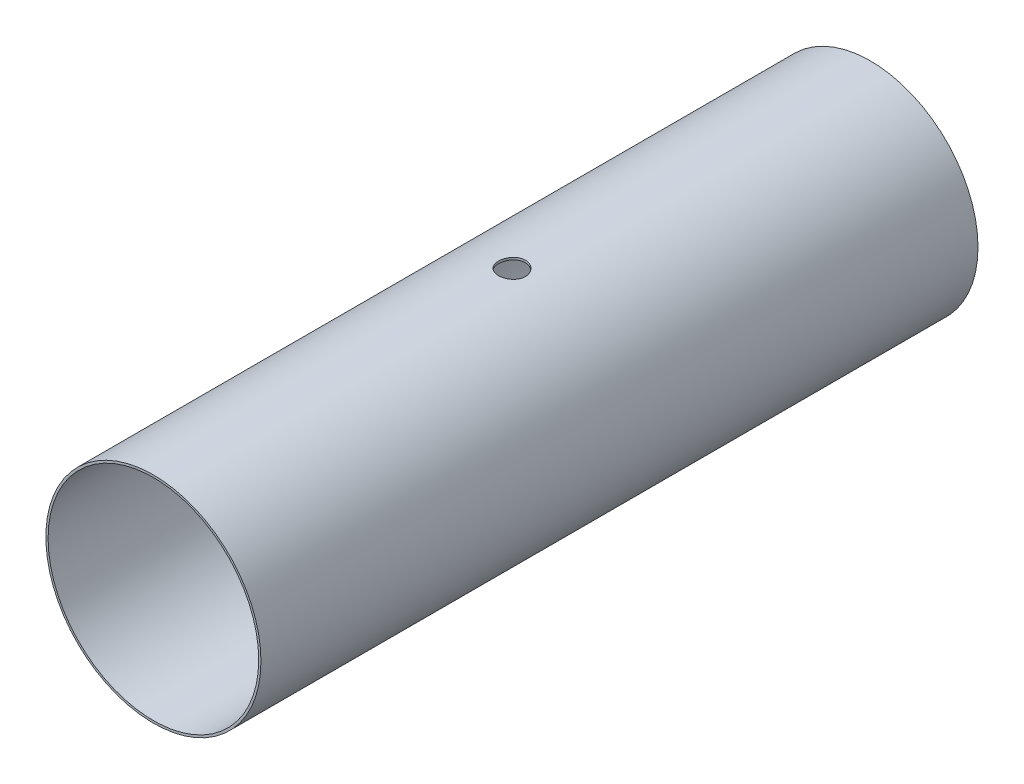
SolidWorks part; units mm, degrees
material "6061-T6 (SS)"
ref_plane "Front Plane" through (0, 0, 0) normal (0, 0, 1) x (1, 0, 0)
ref_plane "Top Plane" through (0, 0, 0) normal (0, 1, 0) x (1, 0, 0)
ref_plane "Right Plane" through (0, 0, 0) normal (1, 0, 0) x (0, 0, -1)
sketch "Sketch1" plane through (0, 0, 0) normal (0, 0, 1) x (1, 0, 0)
  circle A0 centre (0, 0) radius 152.4
  dimension "D1" = 304.8
extrude "Boss-Extrude1" add sketch "Sketch1" along normal blind 1016 contours A0
sketch "Sketch2" plane through (0, 0, 1016) normal (0, 0, 1) x (1, 0, 0)
  circle A0 centre (0, 0) radius 149.225
  dimension "D1" = 298.45
extrude "Cut-Extrude1" cut sketch "Sketch2" against normal blind 1016 contours A0
sketch "Sketch3" plane through (0, 0, 0) normal (0, 1, 0) x (1, 0, 0)
  line L0 (0, 0) -> (0, -25.4) construction
  circle A0 centre (0, -25.4) radius 3.175
  dimension "D1" = 6.35
extrude "Cut-Extrude2" [suppressed] cut sketch "Sketch3" along normal blind 190.5 contours A0
pattern_circular "CirPattern3" [suppressed] count 8 over 360
sketch "Sketch4" plane through (0, 0, 0) normal (0, 1, 0) x (1, 0, 0)
  line L0 (0, 0) -> (0, -508) construction
  circle A0 centre (0, -508) radius 19.05
  dimension "D2" = 38.1
  dimension "D1" = 508
extrude "Cut-Extrude3" cut sketch "Sketch4" against normal blind 459.754 and the other way blind 441.96
equation "\"Rocket Diameter\"= 12in"
equation "\"D1@Sketch1\"=\"Rocket Diameter\""
equation "\"Airframe Thickness\"= 0.125in"
equation "\"Length\" = 40in"
equation "\"D1@Boss-Extrude1\"=\"Length\""
equation "\"D1@Cut-Extrude1\"=\"Length\""
equation "\"Bolt Diameter\"= 0.25in"
equation "\"D1@Sketch3\"=\"Bolt Diameter\""
equation "\"D1@Sketch2\"= \"Rocket Diameter\"-\"Airframe Thickness\"*2"
equation "\"D1@Sketch4\"=\"Length\"/2"
equation "\"relief_diameter\"= 1.5"
equation "\"D2@Sketch4\"=\"relief_diameter\""
